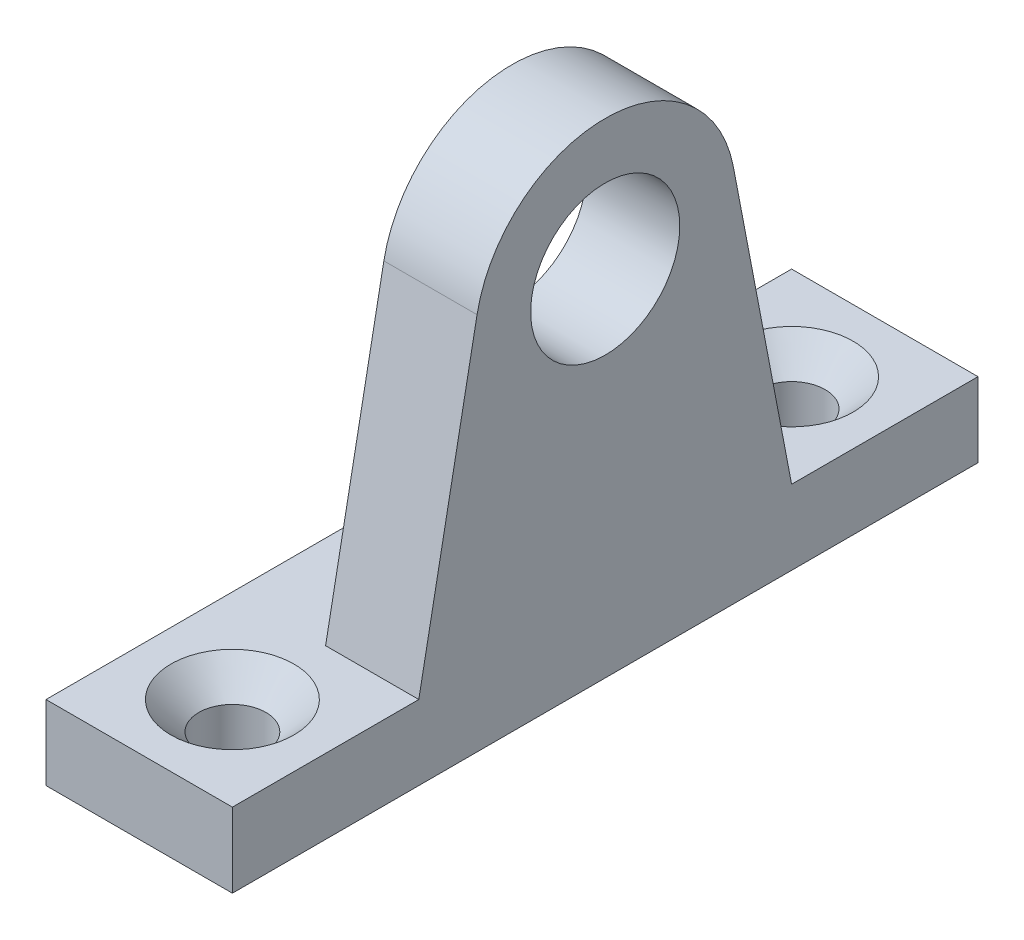
SolidWorks part; units mm, degrees
ref_plane "前视基准面" through (0, 0, 0) normal (0, 0, 1) x (1, 0, 0)
ref_plane "上视基准面" through (0, 0, 0) normal (0, 1, 0) x (1, 0, 0)
ref_plane "右视基准面" through (0, 0, 0) normal (1, 0, 0) x (0, 0, -1)
sketch "草图1" plane through (0, 0, 0) normal (1, 0, 0) x (0, 0, -1)
  line L0 (0, 0) -> (0, 51.6076) construction
  line L1 (-6.875, 20.3167) -> (-10, 4)
  line L2 (-10, 4) -> (-20, 4)
  line L3 (-20, 4) -> (-20, 0)
  line L4 (-20, 0) -> (20, 0)
  line L5 (20, 0) -> (20, 4)
  line L6 (20, 4) -> (10, 4)
  line L7 (10, 4) -> (6.875, 20.3167)
  arc A0 (6.875, 20.3167) -> (-6.875, 20.3167) centre (0, 19) ccw
  circle A1 centre (0, 19) radius 4
  dimension "D1" = 8
  dimension "D2" = 14
  dimension "D3" = 40
  dimension "D4" = 10
  dimension "D5" = 4
  dimension "D6" = 19
extrude "凸台-拉伸1" add sketch "草图1" along normal blind 5
sketch "草图2" plane through (0, 4, 0) normal (0, 1, 0) x (1, 0, 0)
  line L1 (0, 20) -> (-5, 20)
  line L2 (0, 20) -> (0, -20)
  line L3 (0, -20) -> (-5, -20)
  line L4 (-5, 20) -> (-5, -20)
  line L5 (5, -20) -> (0, -20) construction
  dimension "D1" = 5
extrude "凸台-拉伸2" add sketch "草图2" against normal up to surface (4 mm away) up to face at (2.5, 0, 0)
hole_wizard "打孔尺寸(%根据十字)槽半沉头木螺钉的类型1" positions "草图5" profile "草图6" countersink size "M3" standard "GB" end condition through all
sketch "草图5" plane through (0, 4, 0) normal (0, 1, 0) x (1, 0, 0)
  line L0 (0, 6.875) -> (0, -6.875) construction
  line L1 (-3.0876, 0) -> (8.3055, 0) construction
  line L3 (5, 20) -> (-5, 20) construction
  point P0 (0, 15)
  point P2 (0, -15)
  dimension "D1" = 5
sketch "草图6" plane through (0, 4, -15) normal (1, 0, 0) x (0, 0, 1)
  line L0 (0, 0) -> (0, 4)
  line L1 (0, 4) -> (1.8, 4)
  line L2 (1.8, 4) -> (1.8, 1.5)
  line L3 (1.8, 1.5) -> (3.3, 0)
  line L5 (3.3, 0) -> (0, 0)
  line L6 (-1.8, 1.5) -> (-3.3, 0) construction
  line L11 (0, -6.35) -> (0, 107.95) construction
  dimension "通孔孔直径" = 3.6
  dimension "通孔孔深度" = 4
  dimension "近端锥形沉头孔直径" = 6.6
  dimension "近端锥形沉头孔角度" = 90
